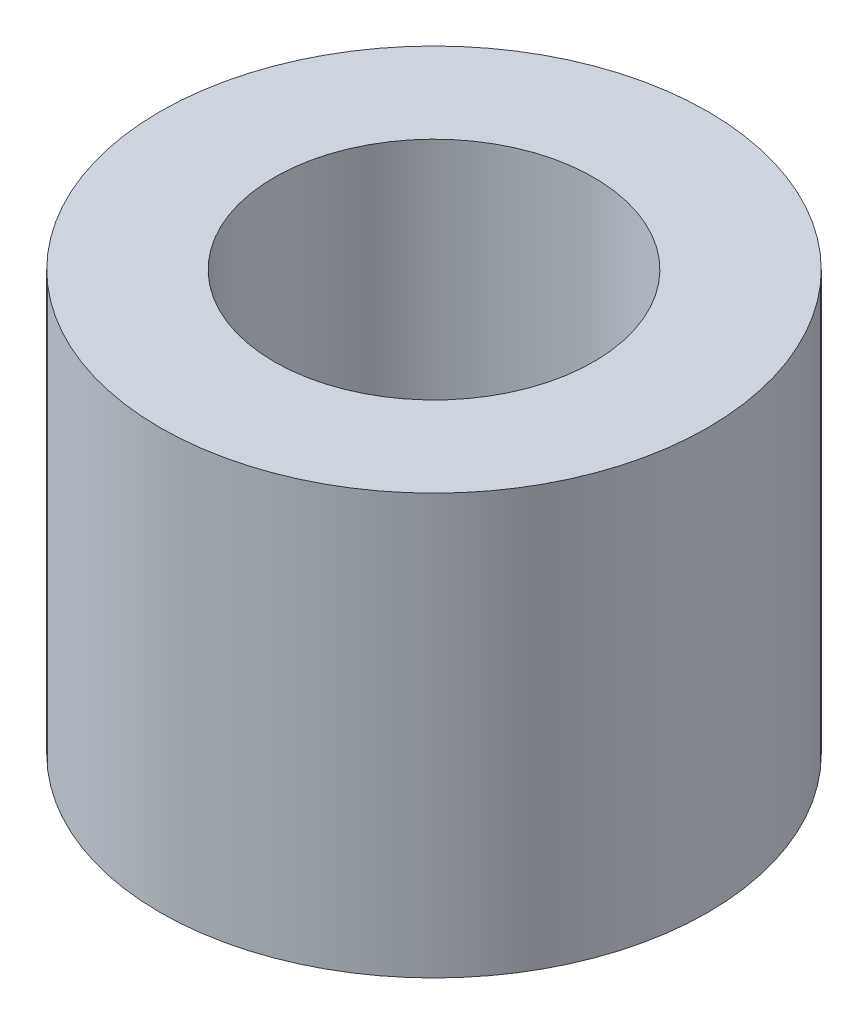
SolidWorks part; units mm, degrees
ref_plane "Front Plane" through (0, 0, 0) normal (0, 0, 1) x (1, 0, 0)
ref_plane "Top Plane" through (0, 0, 0) normal (0, 1, 0) x (1, 0, 0)
ref_plane "Right Plane" through (0, 0, 0) normal (1, 0, 0) x (0, 0, -1)
sketch "Sketch1" plane through (0, 0, 0) normal (0, 1, 0) x (1, 0, 0)
  circle A0 centre (0, 0) radius 1.75
  circle A1 centre (0, 0) radius 3
  dimension "D1" = 3.5
  dimension "D2" = 6
extrude "Boss-Extrude1" add sketch "Sketch1" along normal blind 4.6
